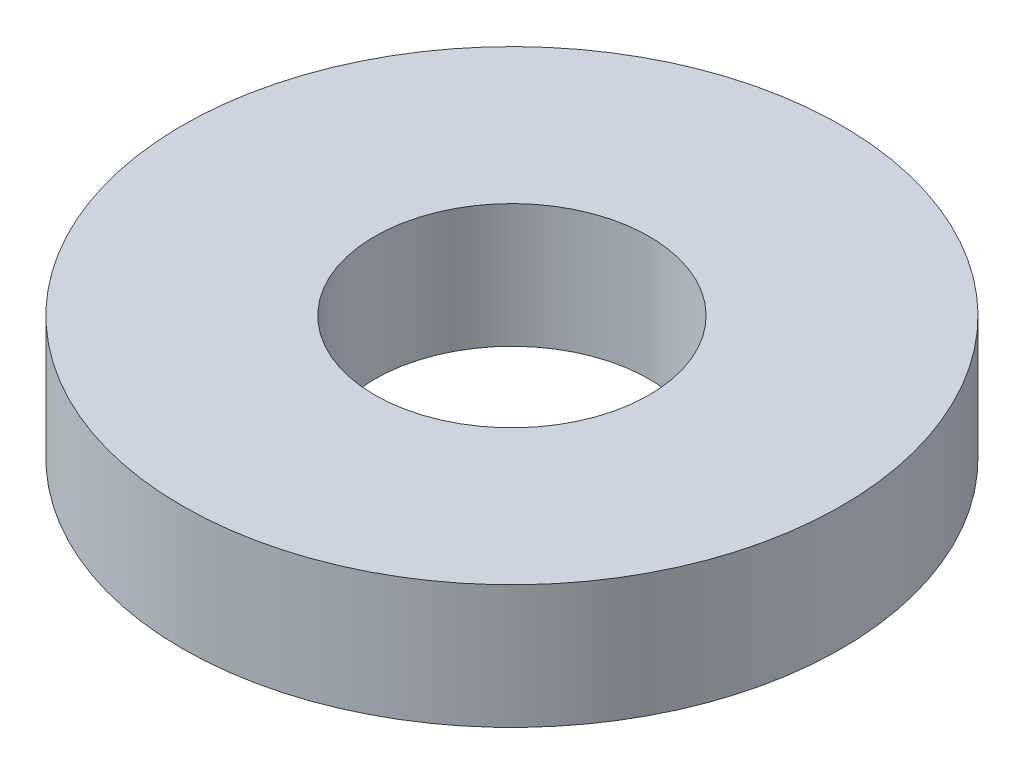
SolidWorks part; units mm, degrees
ref_plane "Front Plane" through (0, 0, 0) normal (0, 0, 1) x (1, 0, 0)
ref_plane "Top Plane" through (0, 0, 0) normal (0, 1, 0) x (1, 0, 0)
ref_plane "Right Plane" through (0, 0, 0) normal (1, 0, 0) x (0, 0, -1)
sketch "Sketch1" plane through (0, 0, 0) normal (0, 1, 0) x (1, 0, 0)
  circle A0 centre (0, 0) radius 9.525
  circle A1 centre (0, 0) radius 3.9688
  dimension "D1" = 7.9375
  dimension "D2" = 19.05
extrude "Extrude1" add sketch "Sketch1" along normal blind 3.5719
split "Split1"
